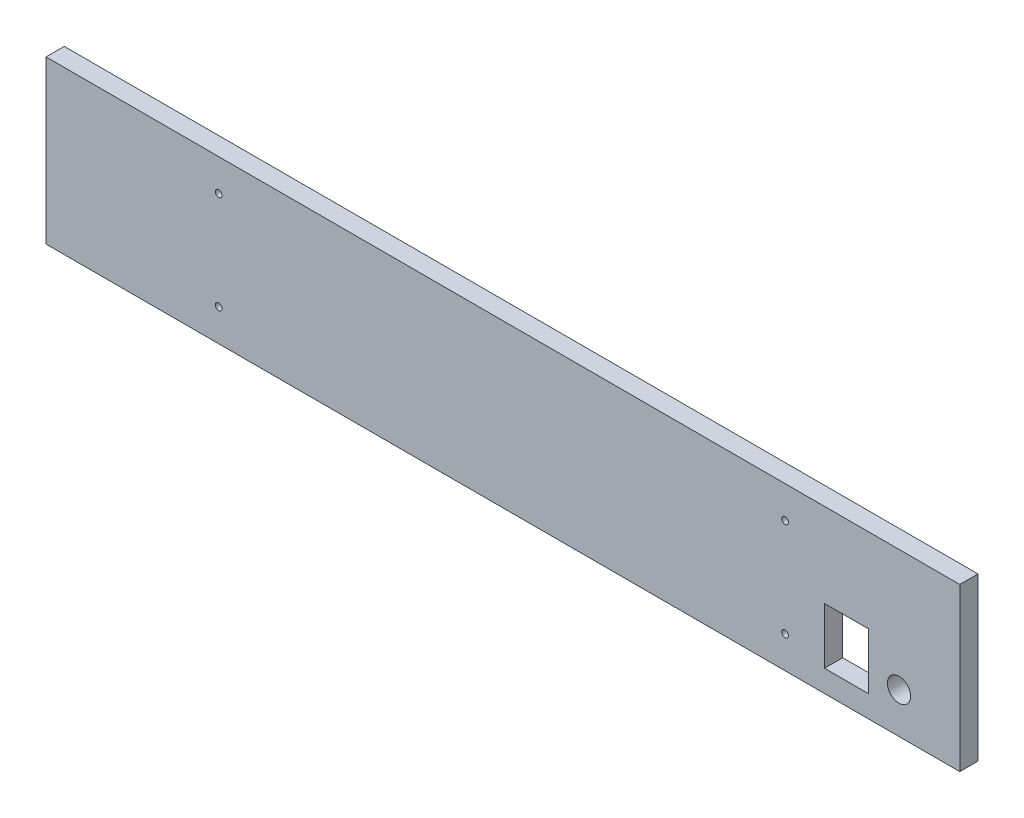
SolidWorks part; units mm, degrees
ref_plane "Płaszczyzna przednia" through (0, 0, 0) normal (0, 0, 1) x (1, 0, 0)
ref_plane "Płaszczyzna górna" through (0, 0, 0) normal (0, 1, 0) x (1, 0, 0)
ref_plane "Płaszczyzna prawa" through (0, 0, 0) normal (1, 0, 0) x (0, 0, -1)
sketch "Szkic1" plane through (0, 0, 0) normal (0, 0, 1) x (1, 0, 0)
  line L1 (0, 0) -> (451, 0)
  line L2 (0, 0) -> (0, 80)
  line L3 (0, 80) -> (451, 80)
  line L4 (451, 0) -> (451, 80)
  dimension "D1" = 451
  dimension "D2" = 80
extrude "Dodanie-wyciągnięcie1" add sketch "Szkic1" against normal blind 9
sketch "Szkic2" plane through (0, 0, 0) normal (0, 0, 1) x (1, 0, 0)
  line L0 (451, 80) -> (0, 80) construction
  line L1 (80.22, 10.79) -> (369.78, 10.79)
  line L2 (80.22, 10.79) -> (80.22, 69.21)
  line L3 (80.22, 69.21) -> (369.78, 69.21)
  line L4 (369.78, 10.79) -> (369.78, 69.21)
  line L6 (451, 0) -> (451, 80) construction
  line L7 (0, 0) -> (451, 0) construction
  line L8 (0, 0) -> (451, 0) construction
  line L9 (406, 10.79) -> (384.2, 10.79)
  line L10 (406, 10.79) -> (406, 38.49)
  line L11 (406, 38.49) -> (384.2, 38.49)
  line L12 (384.2, 10.79) -> (384.2, 38.49)
  line L13 (451, 0) -> (451, 80) construction
  circle A0 centre (85.22, 64.21) radius 1.65
  circle A1 centre (364.78, 64.21) radius 1.65
  circle A2 centre (364.78, 15.79) radius 1.65
  circle A3 centre (85.22, 15.79) radius 1.65
  circle A4 centre (421, 20) radius 5.75
  dimension "D5" = 5
  dimension "D9" = 3.3
  dimension "D10" = 3.3
  dimension "D11" = 3.3
  dimension "D12" = 3.3
  dimension "D17" = 11.5
  dimension "D1" = 289.56
  dimension "D2" = 58.42
  dimension "D3" = 10.79
  dimension "D4" = 80.22
  dimension "D6" = 5
  dimension "D7" = 5
  dimension "D8" = 5
  dimension "D13" = 5
  dimension "D14" = 5
  dimension "D15" = 5
  dimension "D16" = 5
  dimension "D18" = 30
  dimension "D19" = 20
  dimension "D20" = 21.8
  dimension "D21" = 27.7
  dimension "D22" = 10.79
  dimension "D23" = 45
extrude "Wytnij-wyciągnięcie1" cut sketch "Szkic2" against normal blind 10 contours L12 L9 L10 L11 | A4 | A1 | A2 | A0 | A3
